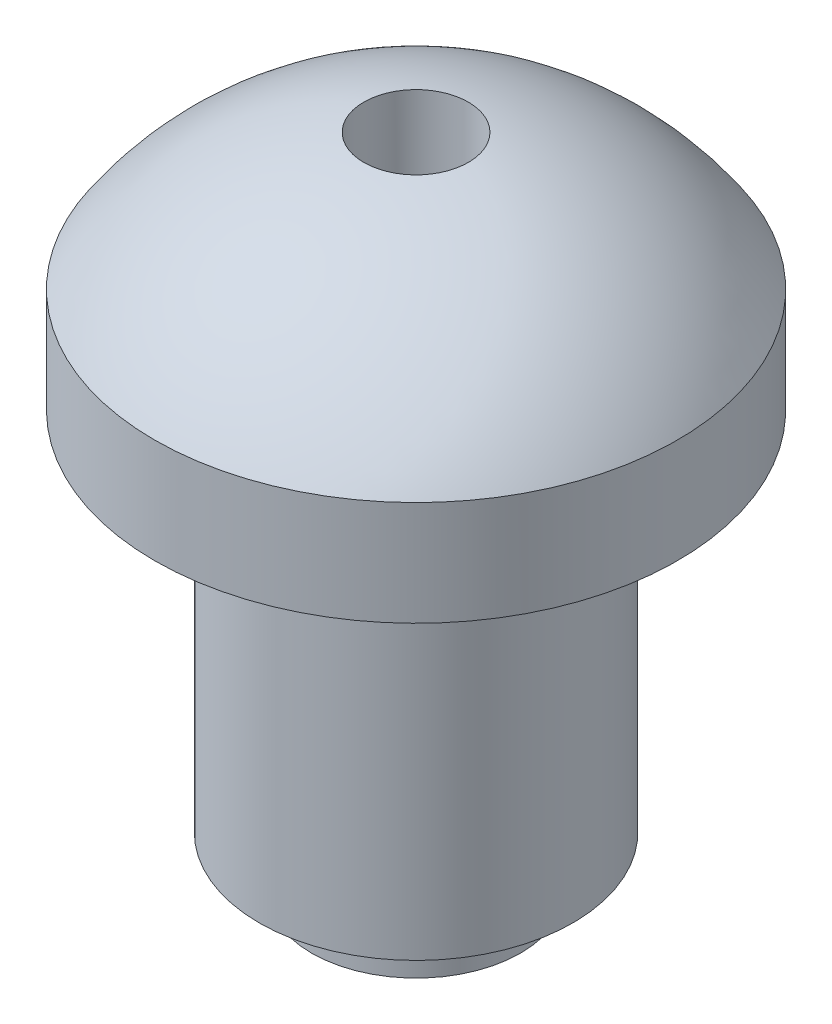
SolidWorks part; units mm, degrees
ref_plane "Front Plane" through (0, 0, 0) normal (0, 0, 1) x (1, 0, 0)
ref_plane "Top Plane" through (0, 0, 0) normal (0, 1, 0) x (1, 0, 0)
ref_plane "Right Plane" through (0, 0, 0) normal (1, 0, 0) x (0, 0, -1)
sketch "Sketch1" plane through (0, 0, 0) normal (0, 0, 1) x (1, 0, 0)
  line L0 (0, 85.0826) -> (0, -84.278) construction
  line L1 (0, 0) -> (-3, 0)
  line L2 (-3, 0) -> (-3, 7)
  line L3 (-2, 0) -> (-2, -1)
  line L4 (-2, -1) -> (0, -1)
  line L5 (0, 7) -> (-5, 7)
  line L6 (-5, 7) -> (-5, 9)
  line L7 (-5, 9) -> (0, 9)
  line L8 (0, 11.6834) -> (-1, 11.6834)
  line L9 (-1, 11.6834) -> (-1, 9.6834)
  line L10 (-1, 9.6834) -> (0, 9.6834)
  arc A1 (0, 11.6834) -> (-5, 9) centre (0, 5.6834) ccw
  dimension "D8" = 2
  dimension "D1" = 3
  dimension "D2" = 2
  dimension "D3" = 1
  dimension "D4" = 7
  dimension "D5" = 5
  dimension "D6" = 2
  dimension "D9" = 1
revolve "Revolve2" add sketch "Sketch1" angle 360 about L0
